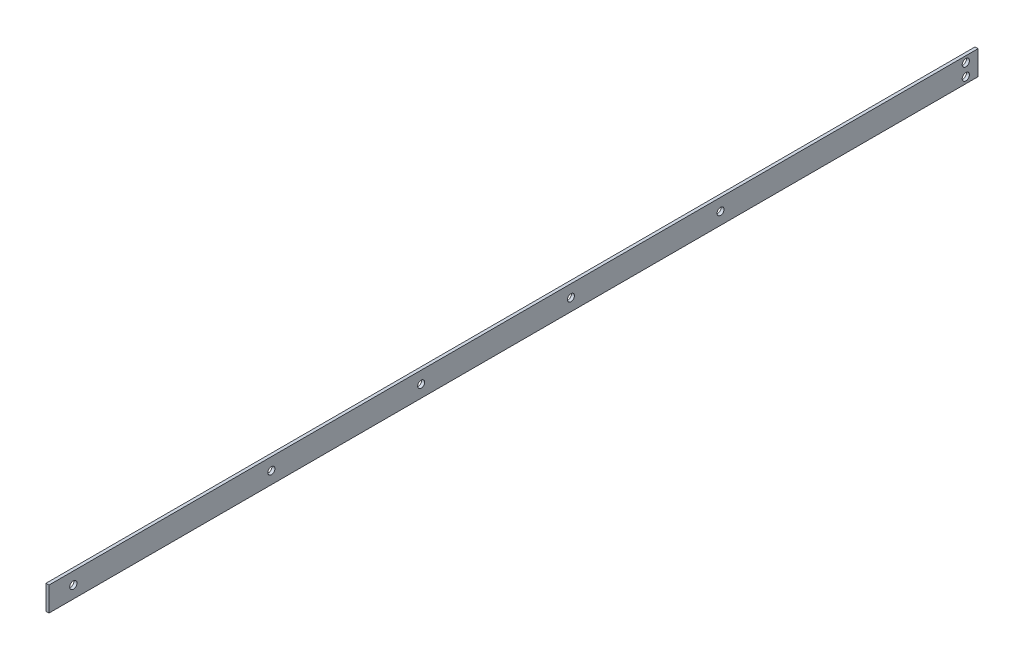
SolidWorks part; units mm, degrees
ref_plane "Front Plane" through (0, 0, 0) normal (0, 0, 1) x (1, 0, 0)
ref_plane "Top Plane" through (0, 0, 0) normal (0, 1, 0) x (1, 0, 0)
ref_plane "Right Plane" through (0, 0, 0) normal (1, 0, 0) x (0, 0, -1)
sketch "Sketch1" plane through (0, 0, 0) normal (0, 0, 1) x (1, 0, 0)
  line L1 (0, 0) -> (1.5875, 0)
  line L2 (0, 0) -> (0, 12.7)
  line L3 (0, 12.7) -> (1.5875, 12.7)
  line L4 (1.5875, 0) -> (1.5875, 12.7)
  dimension "D1" = 1.5875
  dimension "D2" = 12.7
extrude "Boss-Extrude1" add sketch "Sketch1" along normal blind 485.14
hole_wizard "#6 Clearance Hole2" positions "Sketch3" profile "Sketch2" hole size "#6" standard "ANSI Inch" end condition through all
sketch "Sketch3" plane through (1.5875, 0, 0) normal (1, 0, 0) x (0, 0, -1)
  line L0 (0, 0) -> (0, 12.7) construction
  line L1 (-485.14, 12.7) -> (0, 12.7) construction
  line L2 (-485.14, 0) -> (0, 0) construction
  point P0 (-6.35, 9.525)
  point P2 (-6.35, 3.175)
  dimension "D1" = 6.35
  dimension "D2" = 6.35
  dimension "D3" = 3.175
  dimension "D4" = 3.175
sketch "Sketch2" plane through (1.5875, 9.525, 6.35) normal (0, 1, 0) x (0, 0, -1)
  line L0 (0, 0) -> (0, 1.5875)
  line L1 (0, 1.5875) -> (1.8986, 1.5875)
  line L2 (1.8986, 1.5875) -> (1.8986, 0)
  line L5 (1.8986, 0) -> (0, 0)
  line L11 (0, -6.35) -> (0, 107.95) construction
  dimension "Thru Hole Dia." = 3.7973
  dimension "Thru Hole Depth" = 1.5875
hole_wizard "#6 Clearance Hole1" positions "Sketch5" profile "Sketch4" hole size "#6" standard "ANSI Inch" end condition through all
sketch "Sketch5" plane through (1.5875, 0, 0) normal (1, 0, 0) x (0, 0, -1)
  line L0 (-485.14, 0) -> (-485.14, 12.7) construction
  line L1 (-485.14, 12.7) -> (0, 12.7) construction
  point P0 (-472.44, 6.35)
  dimension "D1" = 12.7
  dimension "D2" = 6.35
sketch "Sketch4" plane through (1.5875, 6.35, 472.44) normal (0, 1, 0) x (0, 0, -1)
  line L0 (0, 0) -> (0, 1.5875)
  line L1 (0, 1.5875) -> (1.8986, 1.5875)
  line L2 (1.8986, 1.5875) -> (1.8986, 0)
  line L5 (1.8986, 0) -> (0, 0)
  line L11 (0, -6.35) -> (0, 107.95) construction
  dimension "Thru Hole Dia." = 3.7973
  dimension "Thru Hole Depth" = 1.5875
hole_wizard "#6 Clearance Hole3" positions "Sketch6" profile "Sketch7" hole size "#6" standard "ANSI Inch" end condition through all
sketch "Sketch6" plane through (1.5875, -24.6313, -47.6504) normal (1, 0, 0) x (0, 0, -1)
  point P0 (-416.6839, 30.9813)
  point P3 (-338.4519, 30.9813)
  point P6 (-260.2199, 30.9813)
  point P9 (-182.0811, 30.9813)
sketch "Sketch7" plane through (1.5875, 6.35, 369.0334) normal (0, 1, 0) x (0, 0, -1)
  line L0 (0, 0) -> (0, 1.5875)
  line L1 (0, 1.5875) -> (1.8288, 1.5875)
  line L2 (1.8288, 1.5875) -> (1.8288, 0)
  line L3 (1.8288, 0) -> (0, 0)
  line L4 (0, -6.35) -> (0, 107.95) construction
  dimension "Thru Hole Dia." = 3.6576
  dimension "Thru Hole Depth" = 1.5875
